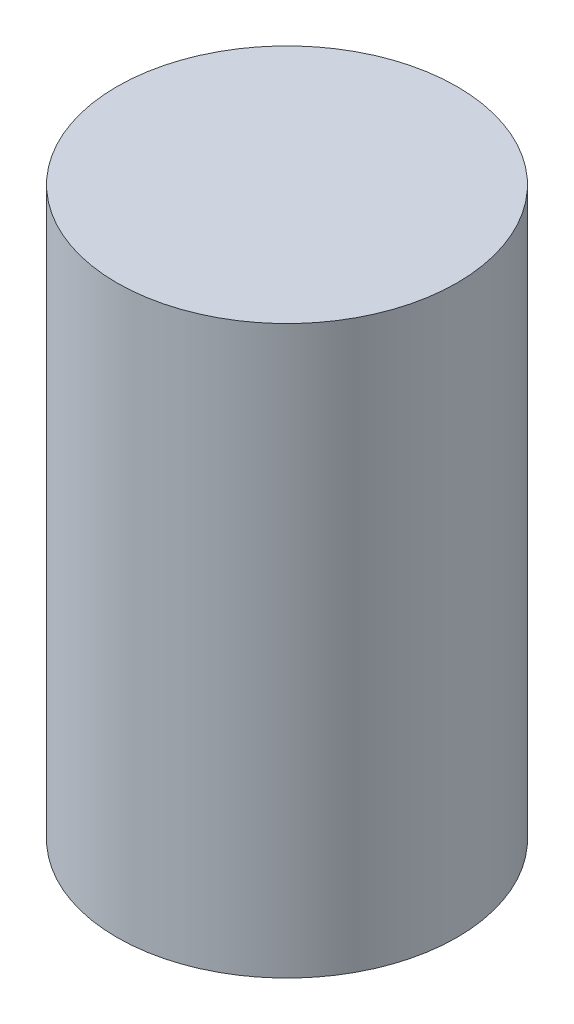
SolidWorks part; units mm, degrees
ref_plane "Front Plane" through (0, 0, 0) normal (0, 0, 1) x (1, 0, 0)
ref_plane "Top Plane" through (0, 0, 0) normal (0, 1, 0) x (1, 0, 0)
ref_plane "Right Plane" through (0, 0, 0) normal (1, 0, 0) x (0, 0, -1)
sketch "Sketch1" plane through (0, 0, 0) normal (0, 1, 0) x (1, 0, 0)
  circle A0 centre (0, 0) radius 1.5
  dimension "D1" = 3
extrude "Boss-Extrude1" add sketch "Sketch1" along normal mid plane 5
